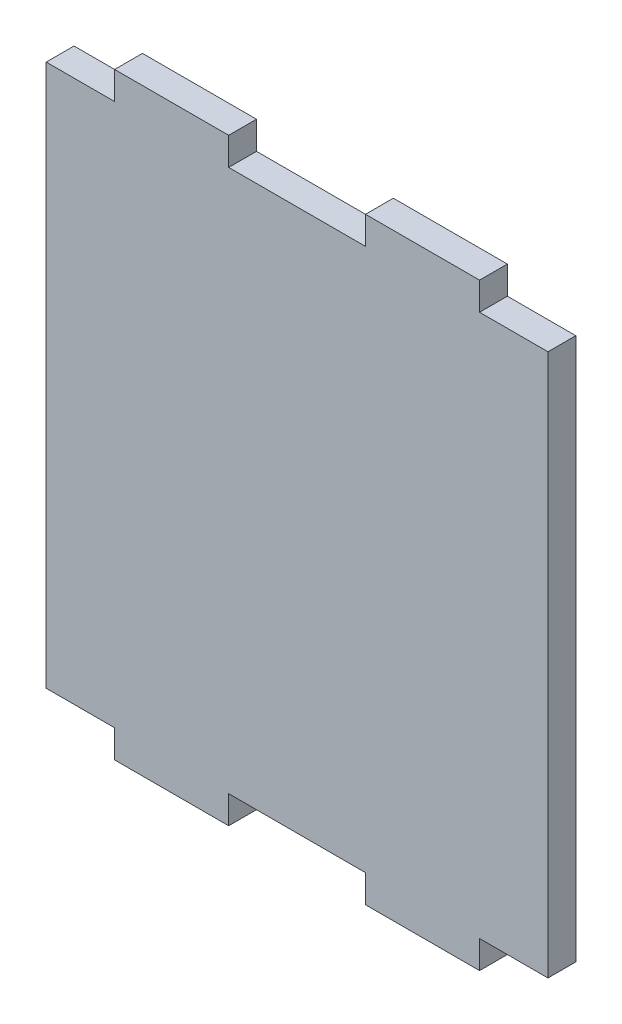
SolidWorks part; units mm, degrees
ref_plane "Alzado" through (0, 0, 0) normal (0, 0, 1) x (1, 0, 0)
ref_plane "Planta" through (0, 0, 0) normal (0, 1, 0) x (1, 0, 0)
ref_plane "Vista lateral" through (0, 0, 0) normal (1, 0, 0) x (0, 0, -1)
sketch "Croquis1" plane through (0, 0, 0) normal (0, 0, 1) x (1, 0, 0)
  line L0 (0, 0) -> (0, -11.7126) construction
  line L1 (-22, -23.78) -> (-16, -23.78)
  line L2 (-22, -23.78) -> (-22, 23.78)
  line L3 (-22, 23.78) -> (-16, 23.78)
  line L4 (22, -23.78) -> (22, 23.78)
  line L5 (-22, -23.78) -> (22, 23.78) construction
  line L6 (-22, 23.78) -> (22, -23.78) construction
  line L7 (0, 0) -> (12.0547, 0) construction
  line L8 (16, -23.78) -> (22, -23.78)
  line L9 (-16, -23.78) -> (-16, -26.22)
  line L10 (6, -23.78) -> (6, -26.22)
  line L11 (6, -26.22) -> (16, -26.22)
  line L12 (16, -23.78) -> (16, -26.22)
  line L13 (-6, -26.22) -> (-16, -26.22)
  line L14 (-6, -23.78) -> (-6, -26.22)
  line L15 (-6, -23.78) -> (6, -23.78)
  line L16 (-16, 23.78) -> (-16, 26.22)
  line L17 (-6, 26.22) -> (-16, 26.22)
  line L18 (-6, 23.78) -> (-6, 26.22)
  line L19 (6, 23.78) -> (6, 26.22)
  line L20 (6, 26.22) -> (16, 26.22)
  line L21 (16, 23.78) -> (16, 26.22)
  line L22 (-6, 23.78) -> (6, 23.78)
  line L23 (16, 23.78) -> (22, 23.78)
  point P0 (0, 0)
  dimension "D1" = 44
  dimension "D2" = 47.56
  dimension "D3" = 6
  dimension "D4" = 10
  dimension "D5" = 2.44
extrude "Saliente-Extruir1" add sketch "Croquis1" along normal blind 2.44
